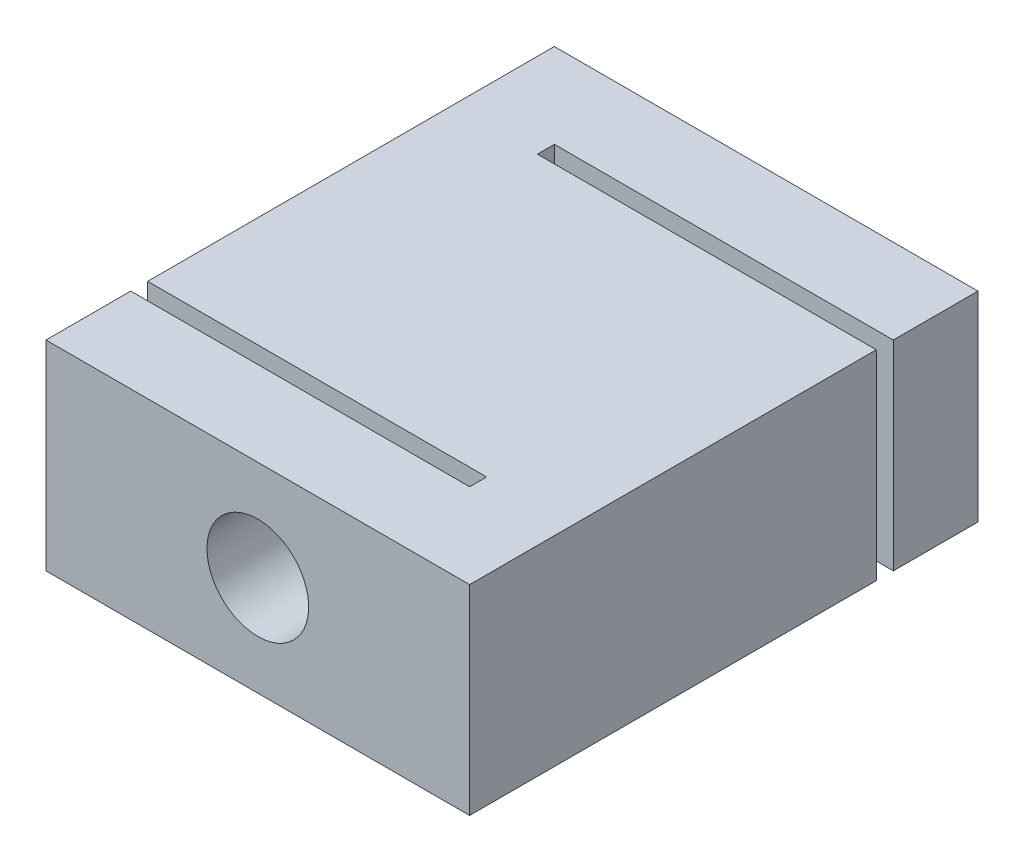
SolidWorks part; units mm, degrees
ref_plane "Front Plane" through (0, 0, 0) normal (0, 0, 1) x (1, 0, 0)
ref_plane "Top Plane" through (0, 0, 0) normal (0, 1, 0) x (1, 0, 0)
ref_plane "Right Plane" through (0, 0, 0) normal (1, 0, 0) x (0, 0, -1)
sketch "草图1" plane through (0, 0, 0) normal (0, 1, 0) x (1, 0, 0)
  line L1 (0, 0) -> (25, 0)
  line L2 (0, 0) -> (0, 30)
  line L3 (0, 30) -> (25, 30)
  line L4 (25, 0) -> (25, 30)
  dimension "D1" = 25
extrude "凸台-拉伸1" add sketch "草图1" along normal blind 11.8
sketch "草图2" plane through (0, 11.8, 0) normal (0, 1, 0) x (1, 0, 0)
  line L0 (25, 30) -> (25, 25)
  line L1 (25, 0) -> (25, 30) construction
  line L2 (25, 25) -> (5, 25)
  line L3 (5, 25) -> (5, 24)
  line L4 (5, 24) -> (25, 24)
  line L5 (25, 24) -> (25, 25)
  line L6 (0, 0) -> (0, 5)
  line L7 (0, 30) -> (0, 0) construction
  line L8 (0, 5) -> (20, 5)
  line L9 (20, 5) -> (20, 6)
  line L10 (20, 6) -> (0, 6)
  line L11 (0, 6) -> (0, 5)
  line M3 (0, 30) -> (0, 0)
  line M5 (25, 0) -> (25, 30)
extrude "切除-拉伸1" cut sketch "草图2" against normal blind 13.5 contours L3 L4 L2 M5 | L9 L10 L8 M3
sketch "草图3" plane through (0, 0, -30) normal (0, 0, -1) x (-1, 0, 0)
  line L0 (-12.5, 11.8) -> (-12.5, 0)
  line L1 (-25, 11.8) -> (0, 11.8) construction
  line L2 (-25, 0) -> (0, 0) construction
  circle A0 centre (-12.5, 5.9) radius 3
extrude "切除-拉伸2" cut sketch "草图3" against normal blind 30 contours L0 A0 | L0 A0
ref_plane "基准面1" through (25, 0, -30) normal (-1, 0, 0) x (0, 0, 1)
